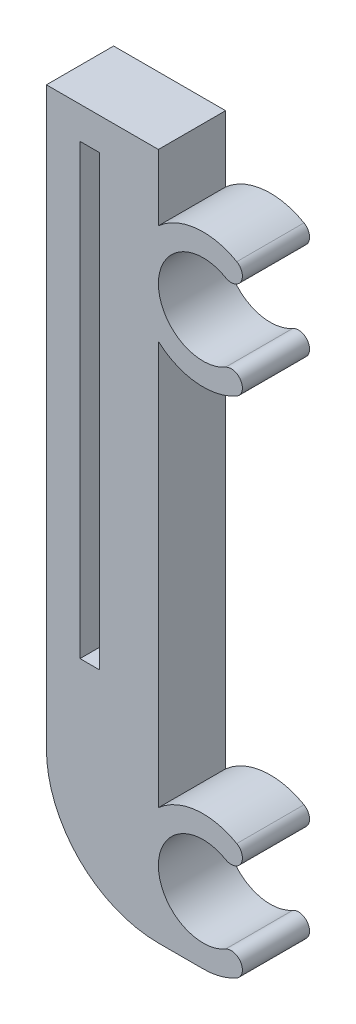
SolidWorks part; units mm, degrees
ref_plane "Front Plane" through (0, 0, 0) normal (0, 0, 1) x (1, 0, 0)
ref_plane "Top Plane" through (0, 0, 0) normal (0, 1, 0) x (1, 0, 0)
ref_plane "Right Plane" through (0, 0, 0) normal (1, 0, 0) x (0, 0, -1)
sketch "Sketch1" plane through (0, 0, 0) normal (0, 0, 1) x (1, 0, 0)
  line L0 (10.073, 10.4721) -> (10.073, 46.5279)
  line L1 (10.073, 61.375) -> (0.073, 61.375)
  line L2 (10.073, 61.375) -> (10.073, 55.4721)
  line L3 (10.073, 10.4721) -> (10.073, -1.6862) construction
  line L4 (14.073, 0) -> (10.073, 0)
  line L5 (0.073, 61.375) -> (0.073, 10)
  line L6 (14.073, 6) -> (14.073, -1.2431) construction
  arc A0 (16.073, 54.4641) -> (17.073, 56.1962) centre (16.573, 55.3301) ccw
  arc A1 (16.073, 54.4641) -> (16.073, 47.5359) centre (14.073, 51) ccw
  arc A2 (17.073, 56.1962) -> (10.073, 55.4721) centre (14.073, 51) ccw
  arc A3 (17.073, 45.8038) -> (16.073, 47.5359) centre (16.573, 46.6699) ccw
  arc A4 (10.073, 46.5279) -> (17.073, 45.8038) centre (14.073, 51) ccw
  arc A5 (16.073, 9.4641) -> (17.073, 11.1962) centre (16.573, 10.3301) ccw
  arc A6 (16.073, 9.4641) -> (16.073, 2.5359) centre (14.073, 6) ccw
  arc A7 (17.073, 11.1962) -> (10.073, 10.4721) centre (14.073, 6) ccw
  arc A8 (17.073, 0.8038) -> (16.073, 2.5359) centre (16.573, 1.6699) ccw
  arc A9 (14.073, 0) -> (17.073, 0.8038) centre (14.073, 6) ccw
  arc A10 (10.073, 0) -> (0.073, 10) centre (10.073, 10) cw
  dimension "D3" = 8.9443
  dimension "D1" = 10
  dimension "D2" = 10
  dimension "D4" = 45
  dimension "D5" = 5.9029
  dimension "D6" = 2
  dimension "D7" = 6.9282
extrude "Boss-Extrude-Base" add sketch "Sketch1" along normal blind 6
sketch "Sketch4" plane through (0, 0, 6) normal (0, 0, 1) x (1, 0, 0)
  line L2 (3.073, 58.5) -> (4.823, 58.5)
  line L3 (3.073, 58.5) -> (3.073, 18.5)
  line L4 (3.073, 18.5) -> (4.823, 18.5)
  line L5 (4.823, 58.5) -> (4.823, 18.5)
  dimension "D1" = 40
  dimension "D2" = 1.75
  dimension "D3" = 2.875
  dimension "D4" = 3
extrude "Cut-Extrude-Slot" cut sketch "Sketch4" against normal blind 4.5
